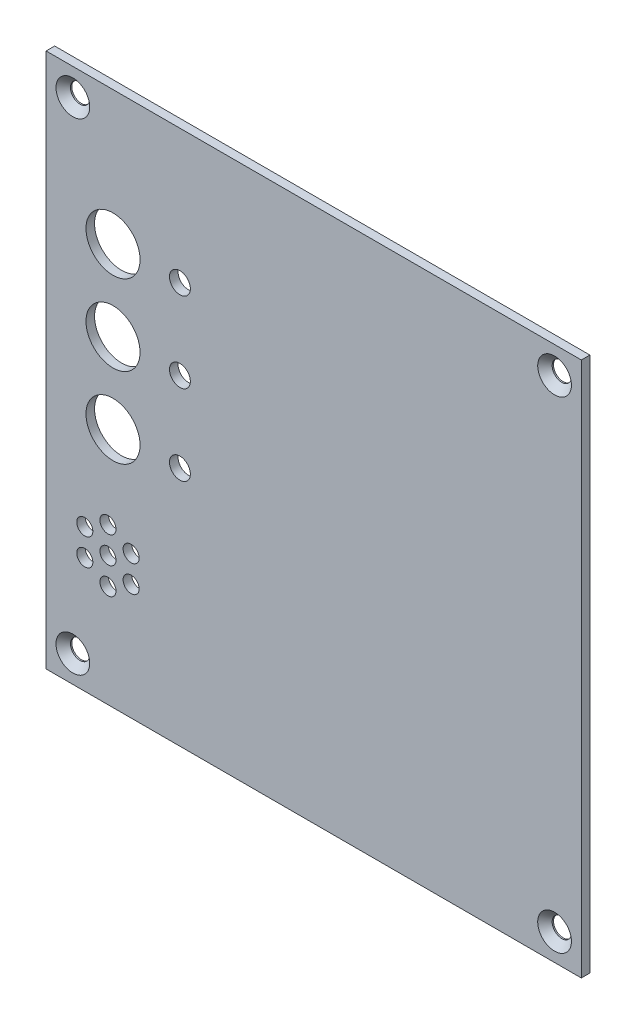
SolidWorks part; units mm, degrees
material "Perspex (TM) Plaque acrylique coulée"
ref_plane "Plan de face" through (0, 0, 0) normal (0, 0, 1) x (1, 0, 0)
ref_plane "Plan de dessus" through (0, 0, 0) normal (0, 1, 0) x (1, 0, 0)
ref_plane "Plan de droite" through (0, 0, 0) normal (1, 0, 0) x (0, 0, -1)
sketch "Esquisse1" plane through (0, 0, 0) normal (0, 0, 1) x (1, 0, 0)
  line L1 (0, 0) -> (100, 0)
  line L2 (0, 0) -> (0, 100)
  line L3 (0, 100) -> (100, 100)
  line L4 (100, 0) -> (100, 100)
  dimension "D1" = 100
  dimension "D2" = 100
extrude "Boss.-Extru.1" add sketch "Esquisse1" along normal blind 1.6
hole_wizard "Fraisage pour vis à tête fraisée M31" positions "Esquisse3D1" profile "Esquisse3" countersink size "M3" standard "ISO" end condition through all
sketch3d "Esquisse3D1"
  line L0 (100, 100, 1.6) -> (0, 100, 1.6) construction
  line L1 (0, 100, 1.6) -> (0, 0, 1.6) construction
  line L2 (100, 0, 1.6) -> (100, 100, 1.6) construction
  line L3 (0, 0, 1.6) -> (100, 0, 1.6) construction
  point P0 (5, 95, 1.6)
  point P2 (95, 95, 1.6)
  point P4 (95, 5, 1.6)
  point P6 (5, 5, 1.6)
  dimension "D1" = 5
  dimension "D2" = 5
  dimension "D3" = 5
  dimension "D4" = 5
  dimension "D5" = 5
  dimension "D6" = 5
  dimension "D7" = 5
  dimension "D8" = 5
sketch "Esquisse3" plane through (5, 95, 1.6) normal (1, 0, 0) x (0, -1, 0)
  line L0 (0, 0) -> (0, 1.6)
  line L1 (0, 1.6) -> (1.8, 1.6)
  line L2 (1.8, 1.6) -> (1.8, 1.35)
  line L3 (1.8, 1.35) -> (3.15, 0)
  line L5 (3.15, 0) -> (0, 0)
  line L6 (-1.8, 1.35) -> (-3.15, 0) construction
  line L11 (0, -6.35) -> (0, 107.95) construction
  dimension "Diamètre du perçage jusqu'au prochain" = 3.6
  dimension "Profondeur du perçage jusqu'au prochain" = 1.6
  dimension "Diamètre du fraisage entrant" = 6.3
  dimension "Angle du fraisage entrant" = 90
sketch "Esquisse4" plane through (0, 0, 1.6) normal (0, 0, 1) x (1, 0, 0)
  line L0 (0, 0) -> (100, 0) construction
  line L2 (0, 100) -> (0, 0) construction
  circle A1 centre (11.557, 24.13) radius 1.5
  circle A3 centre (11.557, 29.13) radius 1.5
  circle A4 centre (15.8871, 26.63) radius 1.5
  circle A5 centre (15.8871, 21.63) radius 1.5
  circle A6 centre (11.557, 19.13) radius 1.5
  circle A7 centre (7.2269, 21.63) radius 1.5
  circle A8 centre (7.2269, 26.63) radius 1.5
  circle A12 centre (12.5, 75) radius 5.05
  circle A13 centre (12.5, 60) radius 5.05
  circle A14 centre (12.5, 45) radius 5.05
  circle A15 centre (25, 75) radius 1.95
  circle A16 centre (25, 60) radius 1.95
  circle A17 centre (25, 45) radius 1.95
  point P25 (11.557, 24.13)
  point P31 (0, 0)
  point P32 (0, 0)
  point P33 (0, 0)
  point P34 (0, 0)
  dimension "D1" = 25
  dimension "D3" = 11.557
  dimension "D5" = 6
  dimension "D7" = 3
  dimension "D10" = 15
  dimension "D8" = 45
  dimension "D2" = 75
  dimension "D4" = 24.13
  dimension "D6" = 11.557
  dimension "D9" = 29.13
  dimension "D11" = 15
  dimension "D12" = 12.5
extrude "Enlèv. mat.-Extru.1" cut sketch "Esquisse4" against normal through all
sketch "Esquisse5" plane through (0, 0, 1.6) normal (0, 0, 1) x (1, 0, 0)
  line L0 (0, 100) -> (0, 0) construction
  line L1 (100, 0) -> (100, 100) construction
  line L2 (0, 0) -> (100, 0) construction
  text T0 "OCCUPÉ" font "Arial" height 3.5
  text T1 "ATTENDEZ" font "Arial" height 3.5
  text T2 "ENTREZ" font "Arial" height 3.5
  text T3 "SONNETTE" font "Arial" height in points 28
  dimension "D7" = 80
  dimension "D1" = 30
  dimension "D2" = 73
  dimension "D3" = 58
  dimension "D4" = 30
  dimension "D5" = 30
  dimension "D6" = 43
  dimension "D8" = 5
